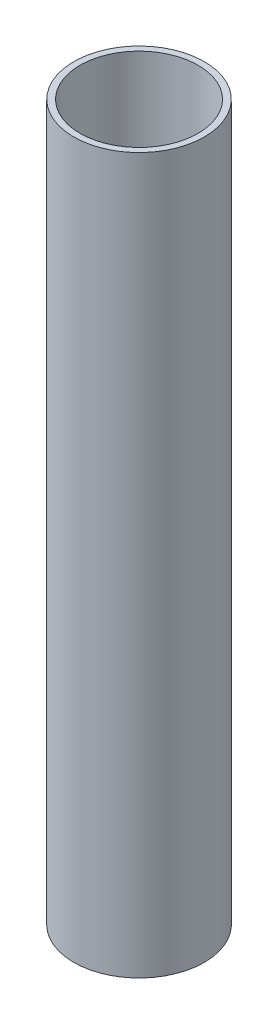
SolidWorks part; units mm, degrees
ref_plane "Front Plane" through (0, 0, 0) normal (0, 0, 1) x (1, 0, 0)
ref_plane "Top Plane" through (0, 0, 0) normal (0, 1, 0) x (1, 0, 0)
ref_plane "Right Plane" through (0, 0, 0) normal (1, 0, 0) x (0, 0, -1)
sketch "Sketch1" plane through (0, 0, 0) normal (0, 1, 0) x (1, 0, 0)
  circle A0 centre (0, 0) radius 19
extrude "Extrude-Thin1" add sketch "Sketch1" along normal blind 230 thin
